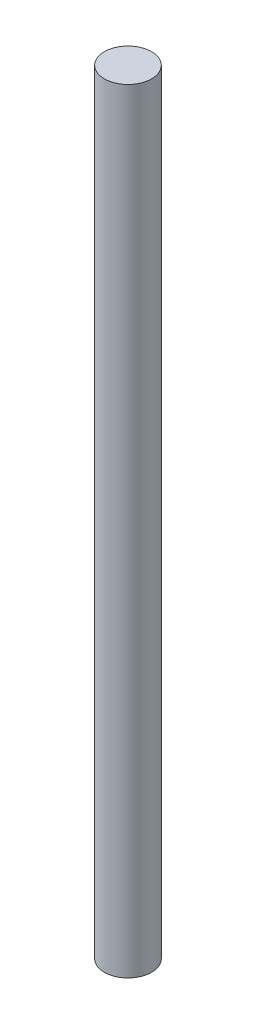
SolidWorks part; units mm, degrees
ref_plane "Front Plane" through (0, 0, 0) normal (0, 0, 1) x (1, 0, 0)
ref_plane "Top Plane" through (0, 0, 0) normal (0, 1, 0) x (1, 0, 0)
ref_plane "Right Plane" through (0, 0, 0) normal (1, 0, 0) x (0, 0, -1)
sketch "Sketch1" plane through (0, 0, 0) normal (0, 1, 0) x (1, 0, 0)
  circle A0 centre (0, 0) radius 152.4
  dimension "D1" = 304.8
extrude "Boss-Extrude1" add sketch "Sketch1" along normal blind 5000
